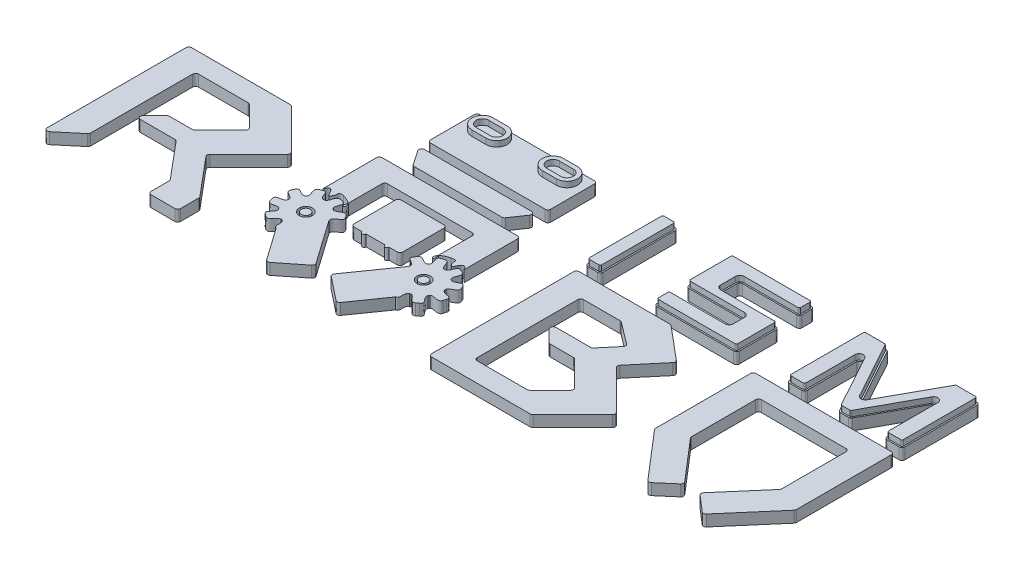
SolidWorks part; units mm, degrees
ref_plane "Front Plane" through (0, 0, 0) normal (0, 0, 1) x (1, 0, 0)
ref_plane "Top Plane" through (0, 0, 0) normal (0, 1, 0) x (1, 0, 0)
ref_plane "Right Plane" through (0, 0, 0) normal (1, 0, 0) x (0, 0, -1)
sketch "Sketch1" plane through (0, 0, 0) normal (0, 1, 0) x (1, 0, 0)
  line L0 (-67.4133, -510.2226) -> (5.6729, -448.896)
  line L1 (0, 0) -> (-73.8412, 0)
  line L2 (9.245, -79.0677) -> (9.245, -441.2356)
  line L4 (-83.8412, -10) -> (-83.8412, -502.5621)
  line L5 (282.9289, -2.9289) -> (423.8976, -143.8976)
  line L6 (0, 0) -> (275.8579, 0)
  line L8 (19.245, -69.0677) -> (195.8847, -69.0677)
  line L11 (202.9558, -71.9967) -> (275.159, -144.1999)
  line L13 (275.159, -158.342) -> (186.1641, -247.337)
  line L14 (423.8976, -158.0397) -> (331.6714, -250.2659)
  line L15 (186.2325, -315.188) -> (293.5722, -443.1105)
  line L16 (179.093, -250.2659) -> (97.3773, -250.2659)
  line L17 (90.3062, -253.1948) -> (48.9562, -294.5449)
  line L18 (56.0272, -311.6159) -> (178.5721, -311.6159)
  line L21 (331.6714, -250.2659) -> (295.4384, -286.4989)
  line L23 (295.9117, -449.5384) -> (295.9117, -514.0072)
  line L24 (305.9117, -524.0072) -> (390.9686, -524.0072)
  line L25 (400.9686, -514.0072) -> (400.9686, -449.5384)
  line L26 (398.6291, -443.1105) -> (285.9829, -308.864)
  line L27 (286.5722, -295.365) -> (295.4384, -286.4989)
  line L28 (0, 0) -> (280, 0) construction
  line L29 (644.2454, 84.4704) -> (678.9487, 33.9401)
  line L32 (692.2294, -70.9322) -> (992.5525, -70.9322)
  line L35 (592.5797, -10) -> (592.5797, -200)
  line L37 (682.2294, -80.9322) -> (682.2294, -200)
  line L38 (627.1808, -232.7708) -> (631.5159, -232.5114)
  line L39 (918.7493, -96.6741) -> (766.0597, -96.6741)
  line L41 (918.7493, -262.9391) -> (890.2593, -262.9391)
  line L42 (756.0597, -106.6741) -> (756.0597, -252.9391)
  line L43 (673.0564, -244.8758) -> (676.5441, -247.4636)
  line L44 (700.4183, -283.637) -> (701.4266, -287.8613)
  line L45 (564.867, -291.7485) -> (564.3362, -296.4789)
  line L46 (611.6308, -367.6713) -> (616.1971, -369.0155)
  line L47 (574.4321, -338.2202) -> (577.0661, -342.1851)
  line L49 (2018.9877, -70.9322) -> (2319.338, -70.9322)
  line L50 (584.257, -252.9861) -> (587.4112, -250.0008)
  line L51 (701.4266, -287.8613) -> (809.7303, -441.9029)
  line L52 (807.761, -455.4916) -> (725.4969, -520.689)
  line L53 (711.1052, -518.6033) -> (630.9254, -404.5626)
  line L54 (630.9254, -404.5626) -> (635.0388, -404.1453)
  line L55 (602.5797, 0) -> (1082.2294, 0)
  line L56 (1002.5524, -80.9593) -> (1002.2294, -200)
  line L57 (1092.2294, -10) -> (1092.2294, -200)
  line L58 (928.7493, -106.6741) -> (928.7493, -252.9391)
  line L59 (1119.942, -291.7485) -> (1120.4729, -296.4789)
  line L60 (1100.552, -252.9861) -> (1097.3979, -250.0008)
  line L61 (1057.6283, -232.7708) -> (1053.2932, -232.5114)
  line L62 (1011.7526, -244.8758) -> (1008.265, -247.4636)
  line L63 (984.3907, -283.637) -> (983.3825, -287.8613)
  line L64 (983.3825, -287.8613) -> (875.0788, -441.9029)
  line L65 (877.048, -455.4916) -> (959.3121, -520.689)
  line L66 (973.7038, -518.6033) -> (1053.8836, -404.5626)
  line L67 (1053.8836, -404.5626) -> (1049.7703, -404.1453)
  line L68 (1073.1783, -367.6713) -> (1068.6119, -369.0155)
  line L69 (1110.377, -338.2202) -> (1107.743, -342.1851)
  line L70 (1395.7191, -78.9646) -> (1525.7223, -78.9646)
  line L71 (1747.7639, -114.3345) -> (1662.457, -215.9993)
  line L75 (1562.7067, -209.6752) -> (1610.2701, -152.9914)
  line L76 (1432.5014, -213.2474) -> (1555.0462, -213.2474)
  line L77 (1466.7804, -271.6684) -> (1425.4303, -230.3184)
  line L78 (1555.5672, -274.5974) -> (1473.8514, -274.5974)
  line L79 (1651.6332, -366.5213) -> (1562.6382, -277.5263)
  line L80 (1579.4299, -452.8666) -> (1651.6332, -380.6634)
  line L81 (1395.7191, -455.7956) -> (1572.3589, -455.7956)
  line L82 (1385.7191, -445.7956) -> (1385.7191, -88.9646)
  line L84 (1292.633, -514.8633) -> (1292.633, -10.8561)
  line L85 (1376.4742, -524.8633) -> (1302.633, -524.8633)
  line L86 (1376.4742, -524.8633) -> (1652.332, -524.8633)
  line L87 (1659.4031, -521.9343) -> (1800.3717, -380.9657)
  line L88 (1800.3717, -366.8236) -> (1708.1455, -274.5974)
  line L89 (1708.1455, -274.5974) -> (1671.9125, -238.3644)
  line L90 (1663.0464, -229.4982) -> (1671.9125, -238.3644)
  line L91 (1302.633, -0.8561) -> (1624.4431, -0.8561)
  line L92 (1608.6052, -138.5602) -> (1531.7178, -80.9613)
  line L93 (1746.5314, -100.2462) -> (1630.871, -3.1956)
  line L94 (1919.338, -10) -> (1919.338, -346.2939)
  line L95 (2008.9877, -80.9322) -> (2008.9877, -308.3808)
  line L96 (1929.338, 0) -> (2408.9877, 0)
  line L99 (1548.3884, 29.6014) -> (1820.3539, 29.6014)
  line L100 (1921.7533, -352.811) -> (2065.1371, -519.6825)
  line L104 (2079.2389, -520.7501) -> (2134.3831, -473.3676)
  line L105 (2135.4507, -459.2658) -> (2011.4031, -314.8979)
  line L107 (2202.875, -459.2658) -> (2326.9227, -314.8979)
  line L108 (2259.0868, -520.7501) -> (2203.9426, -473.3676)
  line L109 (2416.5724, -352.811) -> (2273.1886, -519.6825)
  line L110 (2418.9877, -10) -> (2418.9877, -346.2939)
  line L111 (2329.338, -80.9322) -> (2329.338, -308.3808)
  line L114 (652.4886, 100.1317) -> (1032.3205, 100.1317)
  line L116 (687.1918, 29.6014) -> (997.6172, 29.6014)
  line L117 (1040.5637, 84.4704) -> (1005.8604, 33.9401)
  line L123 (643.4895, 130.7578) -> (1049.9139, 130.7578)
  line L124 (633.4895, 140.7578) -> (633.4895, 295.5348)
  line L125 (643.4895, 305.5348) -> (1049.9139, 305.5348)
  line L126 (1059.9139, 140.7578) -> (1059.9139, 295.5348)
  line L127 (1302.633, 30.0646) -> (1336.3363, 30.0646)
  line L128 (1292.633, 40.0646) -> (1292.633, 295.5348)
  line L129 (1302.633, 305.5348) -> (1336.3363, 305.5348)
  line L130 (1346.3363, 40.0646) -> (1346.3363, 295.5348)
  line L131 (1820.3539, 305.0716) -> (1549.0987, 305.0716)
  line L132 (1830.3539, 295.0716) -> (1830.3539, 262.406)
  line L133 (1820.3539, 252.406) -> (1629.1614, 252.406)
  line L134 (1539.0987, 295.0716) -> (1539.0987, 252.406)
  line L136 (1539.0987, 252.406) -> (1539.0987, 152.1771)
  line L137 (1549.0987, 142.1771) -> (1619.1614, 142.1771)
  line L138 (1619.1614, 242.406) -> (1619.1614, 189.2191)
  line L139 (1619.1614, 142.1771) -> (1741.1936, 142.1771)
  line L141 (1629.1614, 179.2191) -> (1820.3539, 179.2191)
  line L142 (1830.3539, 142.1771) -> (1830.3539, 169.2191)
  line L146 (1741.1936, 82.48) -> (1548.3884, 82.48)
  line L148 (1830.3539, 142.1771) -> (1830.3539, 39.6014)
  line L150 (1751.1936, 132.1771) -> (1751.1936, 92.48)
  line L153 (1538.3884, 72.48) -> (1538.3884, 39.6014)
  line L154 (1751.1936, 30.2777) -> (1751.1936, 30.0646)
  line L155 (794.5498, -262.9391) -> (766.0597, -262.9391)
  line L156 (2366.064, 28.6244) -> (2408.7305, 28.6244)
  line L157 (2018.9877, 29.6014) -> (2061.6542, 29.6014)
  line L158 (2008.9877, 39.6014) -> (2008.9877, 295.0716)
  line L159 (2018.9877, 305.0716) -> (2071.6542, 305.0716)
  line L160 (2071.6542, 39.6014) -> (2071.6542, 213.3118)
  line L161 (2356.064, 38.6244) -> (2356.064, 213.2972)
  line L162 (2356.064, 304.0946) -> (2408.7305, 304.0946)
  line L163 (2418.7305, 38.6244) -> (2418.7305, 294.0946)
  line L164 (2213.8591, 29.1129) -> (2227.9155, 29.0793)
  line L165 (2213.8591, 29.1129) -> (2199.7692, 29.1465)
  line L166 (876.2593, -262.9391) -> (808.5498, -262.9391)
  line L167 (2356.064, 304.0946) -> (2341.9693, 304.0946)
  line L168 (2071.6542, 305.0716) -> (2085.7364, 305.0716)
  line L169 (2094.5022, 299.8841) -> (2205.1125, 98.4115)
  line L170 (2333.2124, 298.9234) -> (2222.6352, 98.3952)
  line L171 (2236.712, 34.2792) -> (2337.2914, 218.0973)
  line L172 (2191.0213, 34.3447) -> (2090.426, 218.1135)
  circle A0 centre (633.4895, -301.8445) radius 23.48
  circle A1 centre (633.4895, -301.8445) radius 15.7007
  circle A2 centre (1051.3195, -301.8445) radius 23.48
  circle A3 centre (1051.3195, -301.8445) radius 15.7007
  arc A4 (766.0597, -96.6741) -> (756.0597, -106.6741) centre (766.0597, -106.6741) ccw
  arc A5 (766.0597, -262.9391) -> (756.0597, -252.9391) centre (766.0597, -252.9391) cw
  arc A6 (918.7493, -262.9391) -> (928.7493, -252.9391) centre (918.7493, -252.9391) ccw
  arc A7 (928.7493, -106.6741) -> (918.7493, -96.6741) centre (918.7493, -106.6741) ccw
  arc A8 (1302.633, 30.0646) -> (1292.633, 40.0646) centre (1302.633, 40.0646) cw
  arc A9 (1336.3363, 30.0646) -> (1346.3363, 40.0646) centre (1336.3363, 40.0646) ccw
  arc A10 (1336.3363, 305.5348) -> (1346.3363, 295.5348) centre (1336.3363, 295.5348) cw
  arc A11 (1302.633, 305.5348) -> (1292.633, 295.5348) centre (1302.633, 295.5348) ccw
  arc A12 (1548.3884, 29.6014) -> (1538.3884, 39.6014) centre (1548.3884, 39.6014) cw
  arc A13 (1548.3884, 82.48) -> (1538.3884, 72.48) centre (1548.3884, 72.48) ccw
  arc A14 (1539.0987, 152.1771) -> (1549.0987, 142.1771) centre (1549.0987, 152.1771) ccw
  arc A15 (1741.1936, 142.1771) -> (1751.1936, 132.1771) centre (1741.1936, 132.1771) cw
  arc A16 (1751.1936, 92.48) -> (1741.1936, 82.48) centre (1741.1936, 92.48) cw
  arc A17 (1830.3539, 39.6014) -> (1820.3539, 29.6014) centre (1820.3539, 39.6014) cw
  arc A18 (1820.3539, 179.2191) -> (1830.3539, 169.2191) centre (1820.3539, 169.2191) cw
  arc A19 (1619.1614, 189.2191) -> (1629.1614, 179.2191) centre (1629.1614, 189.2191) ccw
  arc A20 (1629.1614, 252.406) -> (1619.1614, 242.406) centre (1629.1614, 242.406) ccw
  arc A21 (1830.3539, 262.406) -> (1820.3539, 252.406) centre (1820.3539, 262.406) cw
  arc A22 (1820.3539, 305.0716) -> (1830.3539, 295.0716) centre (1820.3539, 295.0716) cw
  arc A23 (1549.0987, 305.0716) -> (1539.0987, 295.0716) centre (1549.0987, 295.0716) ccw
  arc A24 (2408.7305, 28.6244) -> (2418.7305, 38.6244) centre (2408.7305, 38.6244) ccw
  arc A25 (2366.064, 28.6244) -> (2356.064, 38.6244) centre (2366.064, 38.6244) cw
  arc A26 (2337.2914, 218.0973) -> (2356.064, 213.2972) centre (2346.064, 213.2972) cw
  arc A27 (2408.7305, 304.0946) -> (2418.7305, 294.0946) centre (2408.7305, 294.0946) cw
  arc A28 (2341.9693, 304.0946) -> (2333.2124, 298.9234) centre (2341.9693, 294.0946) ccw
  arc A29 (2222.6352, 98.3952) -> (2205.1125, 98.4115) centre (2213.8784, 103.224) cw
  arc A30 (2227.9155, 29.0793) -> (2236.712, 34.2792) centre (2227.9394, 39.0793) ccw
  arc A31 (2199.7692, 29.1465) -> (2191.0213, 34.3447) centre (2199.7931, 39.1464) cw
  arc A32 (2018.9877, 29.6014) -> (2008.9877, 39.6014) centre (2018.9877, 39.6014) cw
  arc A33 (2061.6542, 29.6014) -> (2071.6542, 39.6014) centre (2061.6542, 39.6014) ccw
  arc A34 (2090.426, 218.1135) -> (2071.6542, 213.3118) centre (2081.6542, 213.3118) ccw
  arc A35 (2085.7364, 305.0716) -> (2094.5022, 299.8841) centre (2085.7364, 295.0716) cw
  arc A36 (2008.9877, 295.0716) -> (2018.9877, 305.0716) centre (2018.9877, 295.0716) cw
  arc A37 (2065.1371, -519.6825) -> (2079.2389, -520.7501) centre (2072.7218, -513.1654) ccw
  arc A38 (2134.3831, -473.3676) -> (2135.4507, -459.2658) centre (2127.866, -465.7829) ccw
  arc A39 (2259.0868, -520.7501) -> (2273.1886, -519.6825) centre (2265.6039, -513.1654) ccw
  arc A40 (2202.875, -459.2658) -> (2203.9426, -473.3676) centre (2210.4597, -465.7829) ccw
  arc A41 (2326.9227, -314.8979) -> (2329.338, -308.3808) centre (2319.338, -308.3808) ccw
  arc A42 (2416.5724, -352.811) -> (2418.9877, -346.2939) centre (2408.9877, -346.2939) ccw
  arc A43 (1919.338, -346.2939) -> (1921.7533, -352.811) centre (1929.338, -346.2939) ccw
  arc A44 (2011.4031, -314.8979) -> (2008.9877, -308.3808) centre (2018.9877, -308.3808) cw
  arc A45 (2018.9877, -70.9322) -> (2008.9877, -80.9322) centre (2018.9877, -80.9322) ccw
  arc A46 (2319.338, -70.9322) -> (2329.338, -80.9322) centre (2319.338, -80.9322) cw
  arc A47 (2408.9877, 0) -> (2418.9877, -10) centre (2408.9877, -10) cw
  arc A48 (1919.338, -10) -> (1929.338, 0) centre (1929.338, -10) cw
  arc A49 (1292.633, -514.8633) -> (1302.633, -524.8633) centre (1302.633, -514.8633) ccw
  arc A50 (1395.7191, -455.7956) -> (1385.7191, -445.7956) centre (1395.7191, -445.7956) cw
  arc A51 (1579.4299, -452.8666) -> (1572.3589, -455.7956) centre (1572.3589, -445.7956) cw
  arc A52 (1652.332, -524.8633) -> (1659.4031, -521.9343) centre (1652.332, -514.8633) ccw
  arc A53 (1800.3717, -380.9657) -> (1800.3717, -366.8236) centre (1793.3007, -373.8946) ccw
  arc A54 (1651.6332, -366.5213) -> (1651.6332, -380.6634) centre (1644.5621, -373.5923) cw
  arc A55 (1555.5672, -274.5974) -> (1562.6382, -277.5263) centre (1555.5672, -284.5974) cw
  arc A56 (1466.7804, -271.6684) -> (1473.8514, -274.5974) centre (1473.8514, -264.5974) ccw
  arc A57 (1562.7067, -209.6752) -> (1555.0462, -213.2474) centre (1555.0462, -203.2474) cw
  arc A58 (1432.5014, -213.2474) -> (1425.4303, -230.3184) centre (1432.5014, -223.2474) ccw
  arc A59 (1395.7191, -78.9646) -> (1385.7191, -88.9646) centre (1395.7191, -88.9646) ccw
  arc A60 (1525.7223, -78.9646) -> (1531.7178, -80.9613) centre (1525.7223, -88.9646) cw
  arc A61 (1608.6052, -138.5602) -> (1610.2701, -152.9914) centre (1602.6096, -146.5635) cw
  arc A62 (1662.457, -215.9993) -> (1663.0464, -229.4982) centre (1670.1175, -222.4272) ccw
  arc A63 (1746.5314, -100.2462) -> (1747.7639, -114.3345) centre (1740.1035, -107.9066) cw
  arc A64 (1630.871, -3.1956) -> (1624.4431, -0.8561) centre (1624.4431, -10.8561) ccw
  arc A65 (1302.633, -0.8561) -> (1292.633, -10.8561) centre (1302.633, -10.8561) ccw
  arc A66 (1002.5524, -80.9593) -> (992.5525, -70.9322) centre (992.5525, -80.9322) ccw
  arc A67 (692.2294, -70.9322) -> (682.2294, -80.9322) centre (692.2294, -80.9322) ccw
  arc A68 (602.5797, 0) -> (592.5797, -10) centre (602.5797, -10) ccw
  arc A69 (1082.2294, 0) -> (1092.2294, -10) centre (1082.2294, -10) cw
  arc A70 (959.3121, -520.689) -> (973.7038, -518.6033) centre (965.5234, -512.8518) ccw
  arc A71 (875.0788, -441.9029) -> (877.048, -455.4916) centre (883.2593, -447.6545) ccw
  arc A72 (809.7303, -441.9029) -> (807.761, -455.4916) centre (801.5498, -447.6545) cw
  arc A73 (725.4969, -520.689) -> (711.1052, -518.6033) centre (719.2857, -512.8518) cw
  arc A74 (678.9487, 33.9401) -> (687.1918, 29.6014) centre (687.1918, 39.6014) ccw
  arc A75 (1005.8604, 33.9401) -> (997.6172, 29.6014) centre (997.6172, 39.6014) cw
  arc A76 (1032.3205, 100.1317) -> (1040.5637, 84.4704) centre (1032.3205, 90.1317) cw
  arc A77 (644.2454, 84.4704) -> (652.4886, 100.1317) centre (652.4886, 90.1317) cw
  arc A78 (643.4895, 130.7578) -> (633.4895, 140.7578) centre (643.4895, 140.7578) cw
  arc A79 (1049.9139, 130.7578) -> (1059.9139, 140.7578) centre (1049.9139, 140.7578) ccw
  arc A80 (1049.9139, 305.5348) -> (1059.9139, 295.5348) centre (1049.9139, 295.5348) cw
  arc A81 (633.4895, 295.5348) -> (643.4895, 305.5348) centre (643.4895, 295.5348) cw
  arc A82 (5.6729, -448.896) -> (9.245, -441.2356) centre (-0.755, -441.2356) ccw
  arc A83 (-67.4133, -510.2226) -> (-83.8412, -502.5621) centre (-73.8412, -502.5621) cw
  arc A84 (-73.8412, 0) -> (-83.8412, -10) centre (-73.8412, -10) ccw
  arc A85 (9.245, -79.0677) -> (19.245, -69.0677) centre (19.245, -79.0677) cw
  arc A86 (195.8847, -69.0677) -> (202.9558, -71.9967) centre (195.8847, -79.0677) cw
  arc A87 (282.9289, -2.9289) -> (275.8579, 0) centre (275.8579, -10) ccw
  arc A88 (285.9829, -308.864) -> (286.5722, -295.365) centre (293.6433, -302.4361) cw
  arc A89 (423.8976, -143.8976) -> (423.8976, -158.0397) centre (416.8265, -150.9686) cw
  arc A90 (275.159, -144.1999) -> (275.159, -158.342) centre (268.0879, -151.2709) cw
  arc A91 (186.1641, -247.337) -> (179.093, -250.2659) centre (179.093, -240.2659) cw
  arc A92 (178.5721, -311.6159) -> (186.2325, -315.188) centre (178.5721, -321.6159) cw
  arc A93 (97.3773, -250.2659) -> (90.3062, -253.1948) centre (97.3773, -260.2659) ccw
  arc A94 (48.9562, -294.5449) -> (56.0272, -311.6159) centre (56.0272, -301.6159) ccw
  arc A95 (295.9117, -514.0072) -> (305.9117, -524.0072) centre (305.9117, -514.0072) ccw
  arc A96 (390.9686, -524.0072) -> (400.9686, -514.0072) centre (390.9686, -514.0072) ccw
  arc A97 (400.9686, -449.5384) -> (398.6291, -443.1105) centre (390.9686, -449.5384) ccw
  arc A98 (293.5722, -443.1105) -> (295.9117, -449.5384) centre (285.9117, -449.5384) cw
  arc A99 (794.5498, -262.9391) -> (808.5498, -262.9391) centre (801.5498, -262.9391) ccw
  arc A100 (876.2593, -262.9391) -> (890.2593, -262.9391) centre (883.2593, -262.9391) ccw
  spline S0 degree 3 poles (592.5797, -200) (601.8533, -178.3961) (613.4412, -189.8909) (624.4356, -216.5121) (639.4689, -193.0338) (630.7109, -180.8951) (651.8729, -185.8034) knots 0 0 0 0 0.3929 0.539017 0.696026 1 1 1 1
  spline S1 degree 3 poles (651.8729, -185.8034) (662.7346, -188.8092) (672.8229, -193.5203) (682.1377, -199.9367) knots 0 0 0 0 0.996727 0.996727 0.996727 0.996727
  spline S2 degree 3 poles (682.1377, -199.9367) (681.5424, -199.6727) (681.5896, -206.618) (679.1587, -210.2744) (678.9821, -215.9526) (682.4681, -221.1633) (688.5494, -215.4858) (686.4302, -207.9731) (684.1539, -203.7368) (682.4586, -200.2101) (682.2294, -200) knots 0 0 0 0 0.110725 0.24808 0.387954 0.472257 0.599066 0.783281 0.956009 0.994592 0.994592 0.994592 0.994592
  spline S3 degree 3 poles (597.0447, -206.243) (611.7208, -199.7047) (610.5352, -220.5558) (623.0124, -233.2971) (627.1808, -232.7708) knots 0 0 0 0 0.720996 1 1 1 1
  spline S4 degree 3 poles (587.4114, -210.6781) (572.2472, -219.933) (593.1819, -236.9537) (587.4112, -250.0008) knots 0 0 0 0 1 1 1 1
  spline S5 degree 2 poles (587.4114, -210.6781) (592.0709, -208.1188) (597.0447, -206.243) knots 0 0 0 1 1 1
  spline S6 degree 3 poles (656.7922, -202.3885) (639.2268, -199.7309) (644.3231, -226.2261) (631.5159, -232.5114) knots 0 0 0 0 1 1 1 1
  spline S7 degree 2 poles (656.7922, -202.3885) (662.0067, -203.423) (667.0226, -205.1832) knots 0 0 0 1 1 1
  spline S8 degree 3 poles (667.0226, -205.1832) (682.4679, -209.6082) (668.1568, -224.819) (669.525, -242.5995) (673.0564, -244.8758) knots 0 0 0 0 0.720996 1 1 1 1
  spline S9 degree 3 poles (715.2694, -240.6355) (703.5219, -227.3088) (690.3951, -250.8811) (676.5441, -247.4636) knots 0 0 0 0 1 1 1 1
  spline S10 degree 2 poles (715.2694, -240.6355) (718.5991, -244.7798) (721.31, -249.3523) knots 0 0 0 1 1 1
  spline S11 degree 3 poles (721.31, -249.3523) (730.2975, -262.6701) (709.5572, -265.1233) (699.1762, -279.6234) (700.4183, -283.637) knots 0 0 0 0 0.720996 1 1 1 1
  spline S12 degree 3 poles (1002.3211, -199.9367) (1002.9164, -199.6727) (1002.8692, -206.618) (1005.3001, -210.2744) (1005.4767, -215.9526) (1001.9907, -221.1633) (995.9094, -215.4858) (998.0286, -207.9731) (1000.3049, -203.7368) (1002.0002, -200.2101) (1002.2294, -200) knots 0 0 0 0 0.110725 0.24808 0.387954 0.472257 0.599066 0.783281 0.956009 0.994592 0.994592 0.994592 0.994592
  spline S13 degree 3 poles (1092.2294, -200) (1082.9557, -178.3961) (1071.3678, -189.8909) (1060.3734, -216.5121) (1045.3401, -193.0338) (1054.0981, -180.8951) (1032.9362, -185.8034) knots 0 0 0 0 0.3929 0.539017 0.696026 1 1 1 1
  spline S14 degree 3 poles (1032.9362, -185.8034) (1021.571, -188.8092) (1011.6359, -193.5203) (1002.3211, -199.9367) knots 0 0 0 0 0.996727 0.996727 0.996727 0.996727
  spline S15 degree 3 poles (1149.1022, -331.3917) (1142.6212, -347.9326) (1122.2238, -330.2716) (1110.377, -338.2202) knots 0 0 0 0 1 1 1 1
  spline S16 degree 2 poles (1149.1022, -331.3917) (1150.8136, -326.3585) (1151.7972, -321.1346) knots 0 0 0 1 1 1
  spline S17 degree 3 poles (1151.7972, -321.1346) (1157.6364, -300.0095) (1125.5013, -313.0705) (1120.4729, -296.4789) knots 0 0 0 0 0.990677 0.990677 0.990677 0.990677
  spline S18 degree 3 poles (1145.218, -261.6255) (1150.8856, -278.4625) (1123.9079, -278.0445) (1119.942, -291.7485) knots 0 0 0 0 1 1 1 1
  spline S19 degree 2 poles (1145.218, -261.6255) (1143.2938, -256.6698) (1140.6893, -252.0358) knots 0 0 0 1 1 1
  spline S20 degree 3 poles (635.0388, -404.1453) (613.2207, -406.2275) (631.6635, -376.8487) (616.1971, -369.0155) knots 0 0 0 0 0.990677 0.990677 0.990677 0.990677
  spline S21 degree 3 poles (577.5762, -387.3325) (593.1733, -395.8376) (597.4463, -369.1973) (611.6308, -367.6713) knots 0 0 0 0 1 1 1 1
  spline S22 degree 2 poles (577.5762, -387.3325) (573.03, -384.5769) (568.9186, -381.2074) knots 0 0 0 1 1 1
  spline S23 degree 3 poles (568.9186, -381.2074) (550.8666, -368.778) (583.8789, -358.1273) (577.0661, -342.1851) knots 0 0 0 0 0.990677 0.990677 0.990677 0.990677
  spline S24 degree 3 poles (535.7068, -331.3917) (542.1879, -347.9326) (562.5853, -330.2716) (574.4321, -338.2202) knots 0 0 0 0 1 1 1 1
  spline S25 degree 2 poles (535.7068, -331.3917) (533.9954, -326.3585) (533.0118, -321.1346) knots 0 0 0 1 1 1
  spline S26 degree 3 poles (533.0118, -321.1346) (527.1727, -300.0095) (559.3077, -313.0705) (564.3362, -296.4789) knots 0 0 0 0 0.990677 0.990677 0.990677 0.990677
  spline S27 degree 3 poles (539.591, -261.6255) (533.9235, -278.4625) (560.9011, -278.0445) (564.867, -291.7485) knots 0 0 0 0 1 1 1 1
  spline S28 degree 2 poles (539.591, -261.6255) (541.5153, -256.6698) (544.1197, -252.0358) knots 0 0 0 1 1 1
  spline S29 degree 3 poles (544.1197, -252.0358) (551.1595, -237.5935) (563.6542, -254.3285) (581.4021, -256.0687) (584.257, -252.9861) knots 0 0 0 0 0.720996 1 1 1 1
  spline S30 degree 3 poles (1140.6893, -252.0358) (1133.6496, -237.5935) (1121.1549, -254.3285) (1103.4069, -256.0687) (1100.552, -252.9861) knots 0 0 0 0 0.720996 1 1 1 1
  spline S31 degree 3 poles (1097.3977, -210.6781) (1112.5619, -219.933) (1091.6271, -236.9537) (1097.3979, -250.0008) knots 0 0 0 0 1 1 1 1
  spline S32 degree 2 poles (1097.3977, -210.6781) (1092.7382, -208.1188) (1087.7644, -206.243) knots 0 0 0 1 1 1
  spline S33 degree 3 poles (1087.7644, -206.243) (1073.0883, -199.7047) (1074.2739, -220.5558) (1061.7967, -233.2971) (1057.6283, -232.7708) knots 0 0 0 0 0.720996 1 1 1 1
  spline S34 degree 3 poles (1028.0169, -202.3885) (1045.5823, -199.7309) (1040.486, -226.2261) (1053.2932, -232.5114) knots 0 0 0 0 1 1 1 1
  spline S35 degree 2 poles (1028.0169, -202.3885) (1022.8023, -203.423) (1017.7864, -205.1832) knots 0 0 0 1 1 1
  spline S36 degree 3 poles (1017.7864, -205.1832) (1002.3412, -209.6082) (1016.6523, -224.819) (1015.2841, -242.5995) (1011.7526, -244.8758) knots 0 0 0 0 0.720996 1 1 1 1
  spline S37 degree 3 poles (969.5396, -240.6355) (981.2872, -227.3088) (994.414, -250.8811) (1008.265, -247.4636) knots 0 0 0 0 1 1 1 1
  spline S38 degree 2 poles (969.5396, -240.6355) (966.21, -244.7798) (963.499, -249.3523) knots 0 0 0 1 1 1
  spline S39 degree 3 poles (963.499, -249.3523) (954.5116, -262.6701) (975.2519, -265.1233) (985.6328, -279.6234) (984.3907, -283.637) knots 0 0 0 0 0.720996 1 1 1 1
  spline S40 degree 3 poles (1049.7703, -404.1453) (1071.5883, -406.2275) (1053.1455, -376.8487) (1068.6119, -369.0155) knots 0 0 0 0 0.990677 0.990677 0.990677 0.990677
  spline S41 degree 3 poles (1107.2328, -387.3325) (1091.6357, -395.8376) (1087.3628, -369.1973) (1073.1783, -367.6713) knots 0 0 0 0 1 1 1 1
  spline S42 degree 2 poles (1107.2328, -387.3325) (1111.7791, -384.5769) (1115.8905, -381.2074) knots 0 0 0 1 1 1
  spline S43 degree 3 poles (1115.8905, -381.2074) (1133.9424, -368.778) (1100.9301, -358.1273) (1107.743, -342.1851) knots 0 0 0 0 0.990677 0.990677 0.990677 0.990677
  point P143 (633.4895, -301.8445)
  point P210 (756.0597, -96.6741)
  point P213 (756.0597, -262.9391)
  point P216 (928.7493, -262.9391)
  point P219 (928.7493, -96.6741)
  point P287 (2008.9877, 29.6014)
  point P342 (2008.9877, 29.6014)
  point P415 (592.5797, 0)
  dimension "D1" = 10
  dimension "D2" = 10
  dimension "D3" = 10
  dimension "D4" = 10
  dimension "D5" = 10
  dimension "D6" = 10
  dimension "D7" = 10
  dimension "D8" = 10
  dimension "D9" = 10
extrude "Boss-Extrude1" add sketch "Sketch1" along normal blind 40
sketch "Sketch3" plane through (0, 0, 0) normal (0, 1, 0) x (1, 0, 0)
  line L0 (633.4895, 218.1463) -> (1059.9139, 218.1463) construction
  line L1 (633.4895, 140.7578) -> (633.4895, 295.5348) construction
  line L2 (1059.9139, 140.7578) -> (1059.9139, 295.5348) construction
  line L7 (946.7017, 261.8406) -> (996.7017, 261.8406) construction
  line L8 (946.7017, 299.2022) -> (996.7017, 299.2022)
  line L9 (946.7017, 224.4789) -> (996.7017, 224.4789)
  line L10 (946.7017, 284.2022) -> (996.7017, 284.2022)
  line L11 (946.7017, 239.4789) -> (996.7017, 239.4789)
  line L12 (746.7017, 261.8406) -> (696.7017, 261.8406) construction
  line L13 (746.7017, 299.2022) -> (696.7017, 299.2022)
  line L14 (746.7017, 224.4789) -> (696.7017, 224.4789)
  line L15 (746.7017, 239.4789) -> (696.7017, 239.4789)
  line L16 (746.7017, 284.2022) -> (696.7017, 284.2022)
  line L28 (1302.633, 35.0646) -> (1336.3363, 35.0646)
  line L29 (1336.3363, 300.5348) -> (1302.633, 300.5348)
  line L30 (1297.633, 295.5348) -> (1297.633, 40.0646)
  line L31 (1341.3363, 40.0646) -> (1341.3363, 295.5348)
  line L64 (1825.3539, 262.406) -> (1825.3539, 295.0716)
  line L65 (1629.1614, 257.406) -> (1820.3539, 257.406)
  line L66 (1820.3539, 300.0716) -> (1549.0987, 300.0716)
  line L67 (1548.3884, 34.6014) -> (1820.3539, 34.6014)
  line L68 (1543.3884, 72.48) -> (1543.3884, 39.6014)
  line L69 (1741.1936, 77.48) -> (1548.3884, 77.48)
  line L70 (1756.1936, 132.1771) -> (1756.1936, 92.48)
  line L71 (1825.3539, 39.6014) -> (1825.3539, 169.2191)
  line L72 (1549.0987, 147.1771) -> (1741.1936, 147.1771)
  line L73 (1820.3539, 174.2191) -> (1629.1614, 174.2191)
  line L74 (1614.1614, 189.2191) -> (1614.1614, 242.406)
  line L75 (1544.0987, 295.0716) -> (1544.0987, 152.1771)
  line L103 (2361.064, 213.2972) -> (2361.064, 38.6244)
  line L104 (2366.064, 33.6244) -> (2408.7305, 33.6244)
  line L105 (2413.7305, 38.6244) -> (2413.7305, 294.0946)
  line L106 (2408.7305, 299.0946) -> (2341.9693, 299.0946)
  line L107 (2337.5909, 296.509) -> (2227.0137, 95.9808)
  line L108 (2232.3257, 36.6793) -> (2332.905, 220.4973)
  line L109 (2199.7812, 34.1464) -> (2227.9274, 34.0793)
  line L110 (2200.7296, 96.0052) -> (2090.1193, 297.4778)
  line L111 (2094.8119, 220.5144) -> (2195.4072, 36.7456)
  line L112 (2085.7364, 300.0716) -> (2018.9877, 300.0716)
  line L113 (2013.9877, 295.0716) -> (2013.9877, 39.6014)
  line L114 (2018.9877, 34.6014) -> (2061.6542, 34.6014)
  line L115 (2066.6542, 39.6014) -> (2066.6542, 213.3118)
  arc A0 (946.7017, 299.2022) -> (946.7017, 224.4789) centre (946.7017, 261.8406) ccw
  arc A1 (996.7017, 224.4789) -> (996.7017, 299.2022) centre (996.7017, 261.8406) ccw
  arc A2 (996.7017, 239.4789) -> (996.7017, 284.2022) centre (996.7017, 261.8406) ccw
  arc A3 (946.7017, 284.2022) -> (946.7017, 239.4789) centre (946.7017, 261.8406) ccw
  arc A4 (746.7017, 299.2022) -> (746.7017, 224.4789) centre (746.7017, 261.8406) cw
  arc A5 (696.7017, 224.4789) -> (696.7017, 299.2022) centre (696.7017, 261.8406) cw
  arc A6 (696.7017, 239.4789) -> (696.7017, 284.2022) centre (696.7017, 261.8406) cw
  arc A7 (746.7017, 284.2022) -> (746.7017, 239.4789) centre (746.7017, 261.8406) cw
  arc A21 (1297.633, 40.0646) -> (1302.633, 35.0646) centre (1302.633, 40.0646) ccw
  arc A22 (1336.3363, 35.0646) -> (1341.3363, 40.0646) centre (1336.3363, 40.0646) ccw
  arc A23 (1341.3363, 295.5348) -> (1336.3363, 300.5348) centre (1336.3363, 295.5348) ccw
  arc A24 (1302.633, 300.5348) -> (1297.633, 295.5348) centre (1302.633, 295.5348) ccw
  arc A57 (1825.3539, 295.0716) -> (1820.3539, 300.0716) centre (1820.3539, 295.0716) ccw
  arc A58 (1820.3539, 257.406) -> (1825.3539, 262.406) centre (1820.3539, 262.406) ccw
  arc A59 (1629.1614, 257.406) -> (1614.1614, 242.406) centre (1629.1614, 242.406) ccw
  arc A60 (1549.0987, 300.0716) -> (1544.0987, 295.0716) centre (1549.0987, 295.0716) ccw
  arc A61 (1544.0987, 152.1771) -> (1549.0987, 147.1771) centre (1549.0987, 152.1771) ccw
  arc A62 (1614.1614, 189.2191) -> (1629.1614, 174.2191) centre (1629.1614, 189.2191) ccw
  arc A63 (1825.3539, 169.2191) -> (1820.3539, 174.2191) centre (1820.3539, 169.2191) ccw
  arc A64 (1756.1936, 132.1771) -> (1741.1936, 147.1771) centre (1741.1936, 132.1771) ccw
  arc A65 (1741.1936, 77.48) -> (1756.1936, 92.48) centre (1741.1936, 92.48) ccw
  arc A66 (1820.3539, 34.6014) -> (1825.3539, 39.6014) centre (1820.3539, 39.6014) ccw
  arc A67 (1543.3884, 39.6014) -> (1548.3884, 34.6014) centre (1548.3884, 39.6014) ccw
  arc A68 (1548.3884, 77.48) -> (1543.3884, 72.48) centre (1548.3884, 72.48) ccw
  arc A96 (2361.064, 38.6244) -> (2366.064, 33.6244) centre (2366.064, 38.6244) ccw
  arc A97 (2408.7305, 33.6244) -> (2413.7305, 38.6244) centre (2408.7305, 38.6244) ccw
  arc A98 (2413.7305, 294.0946) -> (2408.7305, 299.0946) centre (2408.7305, 294.0946) ccw
  arc A99 (2341.9693, 299.0946) -> (2337.5909, 296.509) centre (2341.9693, 294.0946) ccw
  arc A100 (2361.064, 213.2972) -> (2332.905, 220.4973) centre (2346.064, 213.2972) ccw
  arc A101 (2227.9274, 34.0793) -> (2232.3257, 36.6793) centre (2227.9394, 39.0793) ccw
  arc A102 (2195.4072, 36.7456) -> (2199.7812, 34.1464) centre (2199.7931, 39.1464) ccw
  arc A103 (2200.7296, 96.0052) -> (2227.0137, 95.9808) centre (2213.8784, 103.224) ccw
  arc A104 (2090.1193, 297.4778) -> (2085.7364, 300.0716) centre (2085.7364, 295.0716) ccw
  arc A105 (2018.9877, 300.0716) -> (2013.9877, 295.0716) centre (2018.9877, 295.0716) ccw
  arc A106 (2013.9877, 39.6014) -> (2018.9877, 34.6014) centre (2018.9877, 39.6014) ccw
  arc A107 (2061.6542, 34.6014) -> (2066.6542, 39.6014) centre (2061.6542, 39.6014) ccw
  arc A108 (2094.8119, 220.5144) -> (2066.6542, 213.3118) centre (2081.6542, 213.3118) ccw
  point P6 (0, 0)
  point P12 (971.7017, 261.8406)
  point P26 (721.7017, 261.8406)
extrude "Boss-Extrude3" add sketch "Sketch3" along normal blind 60
